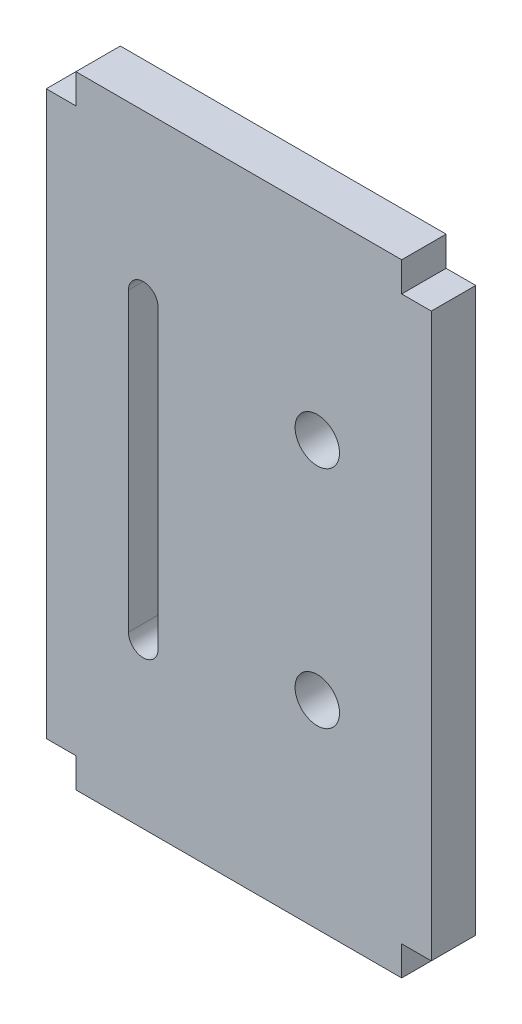
SolidWorks part; units mm, degrees
ref_plane "前视基准面" through (0, 0, 0) normal (0, 0, 1) x (1, 0, 0)
ref_plane "上视基准面" through (0, 0, 0) normal (0, 1, 0) x (1, 0, 0)
ref_plane "右视基准面" through (0, 0, 0) normal (1, 0, 0) x (0, 0, -1)
sketch "草图1" plane through (0, 0, 0) normal (0, 0, 1) x (1, 0, 0)
  line L0 (0, 42.2662) -> (0, -31.4252) construction
  line L1 (11, -21) -> (-11, -21)
  line L2 (11, -21) -> (11, 21)
  line L3 (11, 21) -> (-11, 21)
  line L4 (-11, -21) -> (-11, 21)
  line L5 (11, -21) -> (-11, 21) construction
  line L6 (11, 21) -> (-11, -21) construction
  line L7 (-11, 19) -> (-13, 19)
  line L8 (-11, 19) -> (-11, -19)
  line L9 (-11, -19) -> (-13, -19)
  line L10 (-13, 19) -> (-13, -19)
  line L11 (-47.7492, 0) -> (31.8333, 0) construction
  line L13 (11, 19) -> (13, 19)
  line L14 (11, 19) -> (11, -19)
  line L15 (11, -19) -> (13, -19)
  line L16 (13, 19) -> (13, -19)
  point P0 (0, 0)
  dimension "D1" = 22
  dimension "D2" = 42
  dimension "D3" = 2
  dimension "D4" = 38
  dimension "D5" = 2
extrude "凸台-拉伸1" add sketch "草图1" along normal blind 3 contours L4 L1 L2 L3 | L7 L10 L9 L4 | L16 L13 L2 L15
sketch "草图2" plane through (0, 0, 3) normal (0, 0, 1) x (1, 0, 0)
  line L0 (13, 19) -> (13, -19) construction
  line L1 (11, 21) -> (-11, 21) construction
  line L4 (-6.45, -10) -> (-6.45, 10) construction
  line L5 (-7.45, -10) -> (-7.45, 10)
  line L6 (-5.45, -10) -> (-5.45, 10)
  circle A0 centre (5.3, -7.6) radius 1.5
  circle A1 centre (5.3, 7.6) radius 1.5
  arc A2 (-7.45, -10) -> (-5.45, -10) centre (-6.45, -10) ccw
  arc A3 (-5.45, 10) -> (-7.45, 10) centre (-6.45, 10) ccw
  point P10 (-6.45, 0)
  point P15 (0, 0)
  dimension "D1" = 3
  dimension "D2" = 3
  dimension "D3" = 15.2
  dimension "D4" = 7.7
  dimension "D5" = 13.4
  dimension "D6" = 7.7
  dimension "D7" = 11.75
  dimension "D8" = 1
  dimension "D9" = 20
extrude "切除-拉伸1" cut sketch "草图2" against normal blind 10
